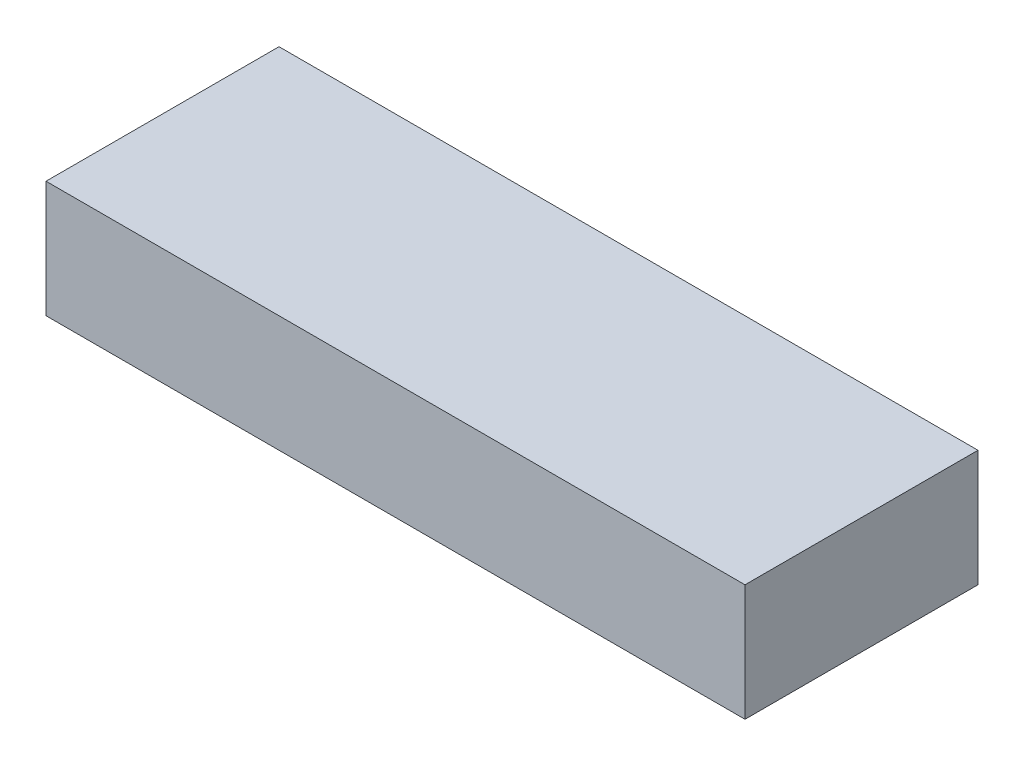
SolidWorks part; units mm, degrees
ref_plane "Front Plane" through (0, 0, 0) normal (0, 0, 1) x (1, 0, 0)
ref_plane "Top Plane" through (0, 0, 0) normal (0, 1, 0) x (1, 0, 0)
ref_plane "Right Plane" through (0, 0, 0) normal (1, 0, 0) x (0, 0, -1)
sketch "Sketch1" plane through (0, 0, 0) normal (0, 1, 0) x (1, 0, 0)
  line L0 (0, -8.25) -> (0, 8.25) construction
  line L5 (15, 5) -> (-15, 5)
  line L6 (15, 5) -> (15, -5)
  line L7 (15, -5) -> (-15, -5)
  line L8 (-15, 5) -> (-15, -5)
  line L9 (-16.5, 0) -> (16.5, 0) construction
  dimension "D3" = 30
  dimension "D4" = 10
  dimension "D5" = 15
  dimension "D6" = 5
extrude "Boss-Extrude1" add sketch "Sketch1" along normal mid plane 5
